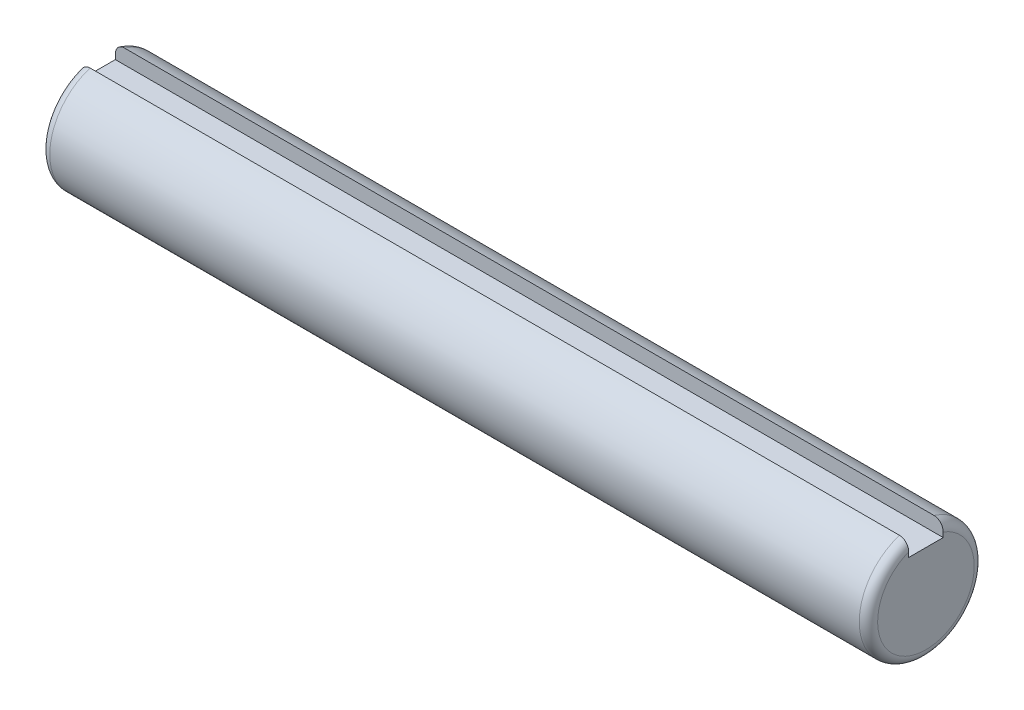
SolidWorks part; units mm, degrees
material "AISI 1020"
ref_plane "Front Plane" through (0, 0, 0) normal (0, 0, 1) x (1, 0, 0)
ref_plane "Top Plane" through (0, 0, 0) normal (0, 1, 0) x (1, 0, 0)
ref_plane "Right Plane" through (0, 0, 0) normal (1, 0, 0) x (0, 0, -1)
sketch "Sketch1" plane through (0, 0, 0) normal (1, 0, 0) x (0, 0, -1)
  circle A0 centre (0, 0) radius 7.9375
  dimension "D1" = 15.875
extrude "Extrude1" add sketch "Sketch1" along normal blind 114.3
sketch "Sketch2" plane through (0, 0, 0) normal (-1, 0, 0) x (0, 0, 1)
  line L0 (0, 8.4685) -> (0, -8.7456) construction
  line L2 (-2.3813, 7.9375) -> (2.3813, 7.9375)
  line L3 (-2.3813, 7.9375) -> (-2.3813, 5.5562)
  line L4 (-2.3813, 5.5562) -> (2.3812, 5.5563)
  line L5 (2.3813, 7.9375) -> (2.3812, 5.5563)
  circle A0 centre (0, 0) radius 7.9375 construction
  dimension "D1" = 4.7625
  dimension "D2" = 2.3813
  dimension "D3" = 2.3813
extrude "Cut-Extrude1" cut sketch "Sketch2" against normal through all
fillet "Fillet1" radius 1.27 2 edges at (0, -7.9375, 0) (114.3, -7.9375, 0)
